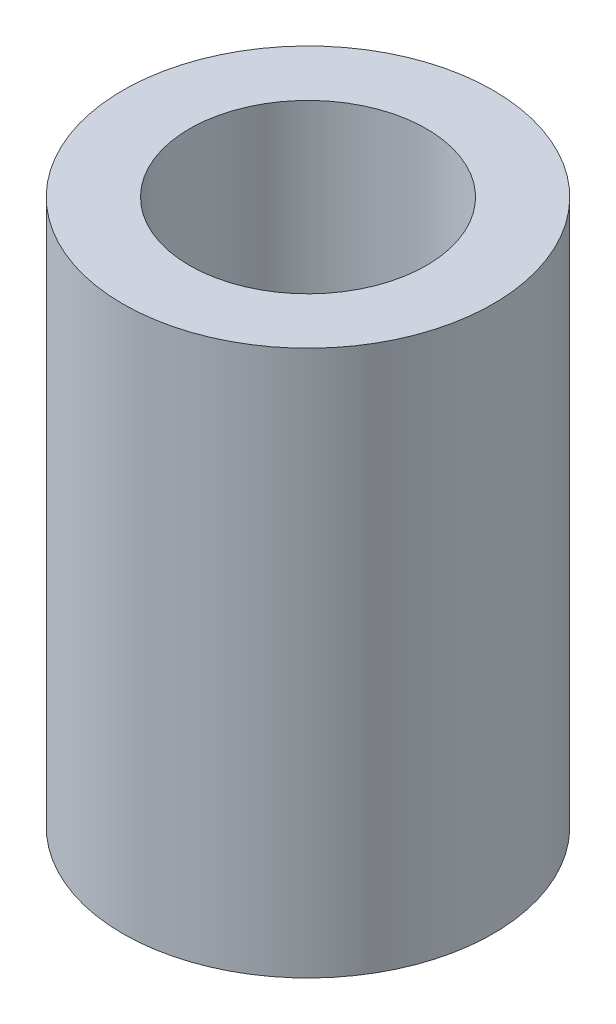
SolidWorks part; units mm, degrees
ref_plane "Front Plane" through (0, 0, 0) normal (0, 0, 1) x (1, 0, 0)
ref_plane "Top Plane" through (0, 0, 0) normal (0, 1, 0) x (1, 0, 0)
ref_plane "Right Plane" through (0, 0, 0) normal (1, 0, 0) x (0, 0, -1)
sketch "Sketch1" plane through (0, 0, 0) normal (0, 1, 0) x (1, 0, 0)
  circle A0 centre (0, 0) radius 1.6
  circle A1 centre (0, 0) radius 2.5
  dimension "D1" = 3.2
  dimension "D2" = 5
extrude "Boss-Extrude1" add sketch "Sketch1" along normal blind 7.366
